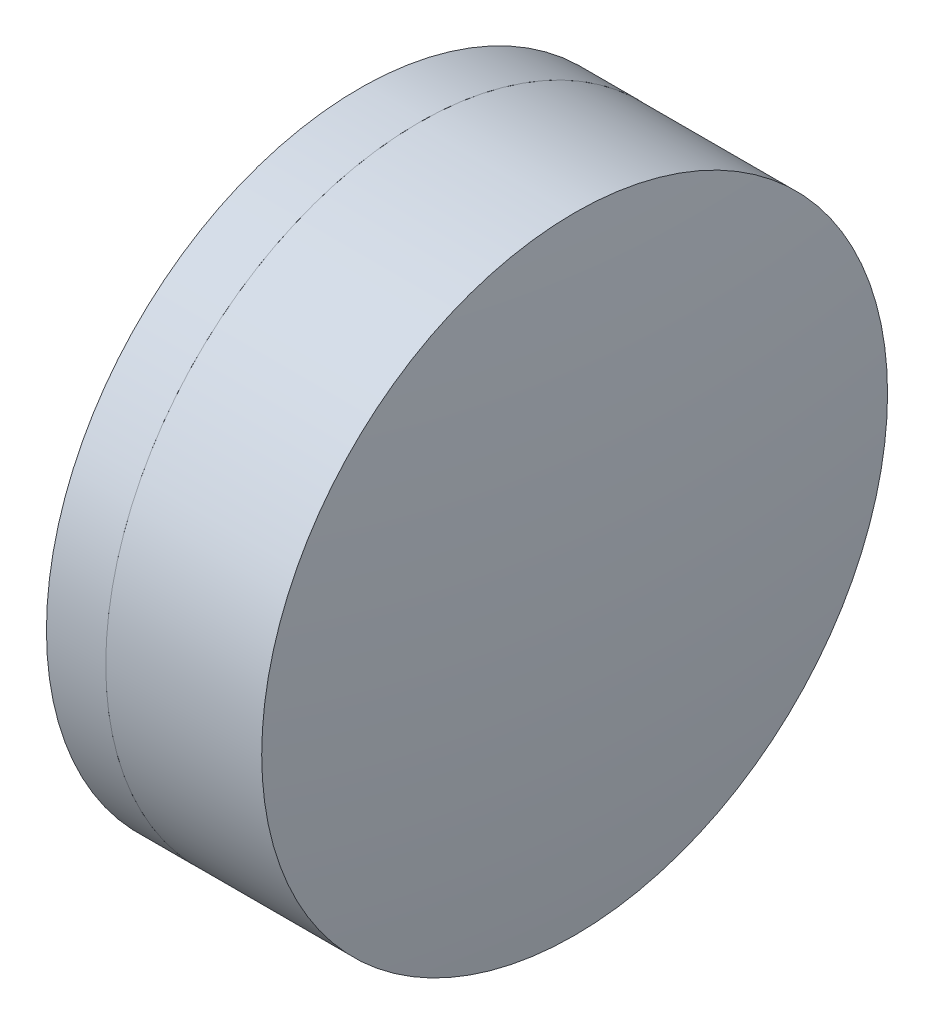
SolidWorks part; units mm, degrees
ref_plane "前视基准面" through (0, 0, 0) normal (0, 0, 1) x (1, 0, 0)
ref_plane "上视基准面" through (0, 0, 0) normal (0, 1, 0) x (1, 0, 0)
ref_plane "右视基准面" through (0, 0, 0) normal (1, 0, 0) x (0, 0, -1)
sketch "草图1" plane through (0, 0, 0) normal (0, 1, 0) x (1, 0, 0)
  line L0 (-0.8161, 0) -> (26.6816, 0) construction
  line L1 (18.4948, -12.7) -> (20.9019, -12.7)
  line L2 (18.4948, 12.7) -> (20.9019, 12.7)
  arc A0 (20.9019, -12.7) -> (20.9019, 12.7) centre (8.3302, 0) ccw
  arc A1 (18.4948, 12.7) -> (18.4948, -12.7) centre (37.8502, 0) ccw
  point P10 (14.7002, 0)
  point P11 (26.2002, 0)
  dimension "D3" = 23.15
  dimension "D4" = 17.87
  dimension "D1" = 12.7
  dimension "D2" = 12.7
  dimension "D5" = 11.5
revolve "旋转1" add sketch "草图1" angle 360 about L0
sketch "草图2" plane through (0, 0, 0) normal (0, 1, 0) x (1, 0, 0)
  line L0 (-0.5519, 0) -> (34.9089, 0) construction
  line L2 (20.9019, 12.7) -> (27.2308, 12.7)
  line L3 (20.9019, -12.7) -> (27.2308, -12.7)
  arc A0 (27.2308, -12.7) -> (27.2308, 12.7) centre (-77.1998, 0) ccw
  arc A1 (20.9019, -12.7) -> (20.9019, 12.7) centre (8.3302, 0) ccw construction
  arc A2 (20.9019, -12.7) -> (20.9019, 12.7) centre (8.3302, 0) ccw
  point P4 (26.2002, 0)
  point P12 (28.0002, 0)
  dimension "D1" = 105.2
  dimension "D2" = 1.8
revolve "旋转2" add sketch "草图2" angle 360 about L0
